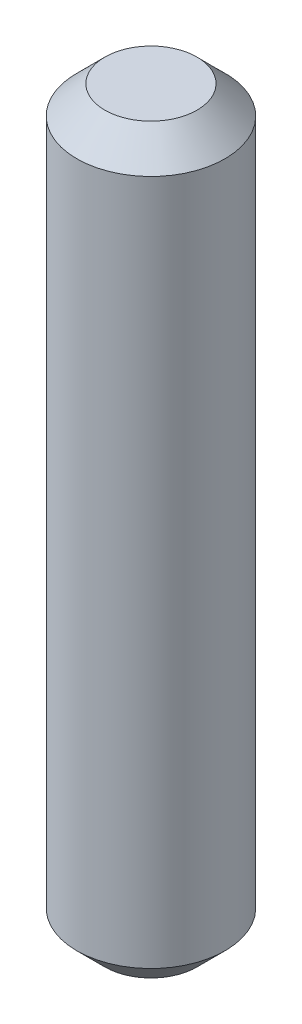
SolidWorks part; units mm, degrees
ref_plane "Front Plane" through (0, 0, 0) normal (0, 0, 1) x (1, 0, 0)
ref_plane "Top Plane" through (0, 0, 0) normal (0, 1, 0) x (1, 0, 0)
ref_plane "Right Plane" through (0, 0, 0) normal (1, 0, 0) x (0, 0, -1)
sketch "Sketch1" plane through (0, 0, 0) normal (0, 1, 0) x (1, 0, 0)
  circle A0 centre (0, 0) radius 1.585
  dimension "D1" = 3.17
extrude "Boss-Extrude1" add sketch "Sketch1" along normal mid plane 15.87
chamfer "Chamfer1" distance 0.6 angle 45 2 edges at (0, -7.935, 1.585) (0, 7.935, 1.585)
